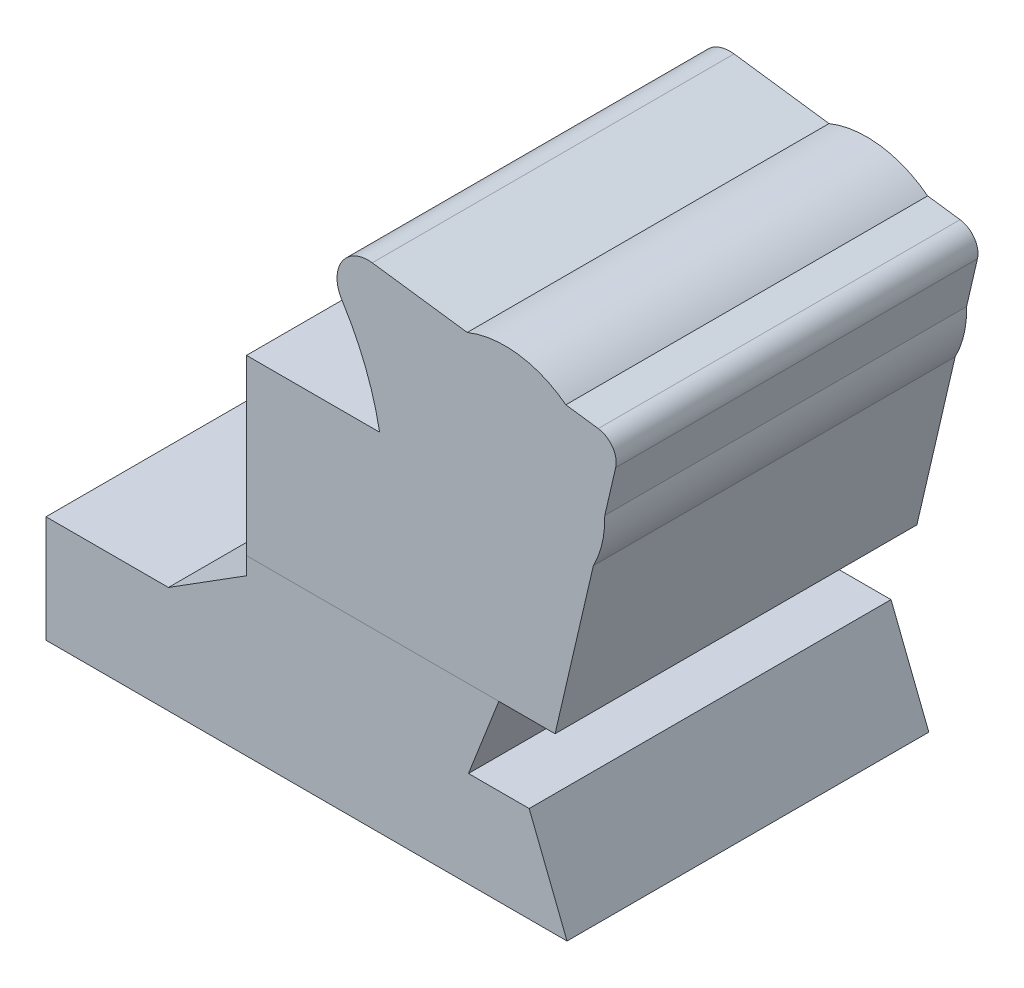
SolidWorks part; units mm, degrees
ref_plane "前视基准面" through (0, 0, 0) normal (0, 0, 1) x (1, 0, 0)
ref_plane "上视基准面" through (0, 0, 0) normal (0, 1, 0) x (1, 0, 0)
ref_plane "右视基准面" through (0, 0, 0) normal (1, 0, 0) x (0, 0, -1)
sketch "草图1" plane through (0, 0, 0) normal (0, 0, 1) x (1, 0, 0)
  line L1 (0, 29.5569) -> (33.8411, 29.5569)
  line L2 (116.7701, 26.4939) -> (125.1562, 47.9624)
  line L3 (152.6325, 126.9813) -> (90.1698, 135.4275)
  line L6 (89.0201, 126.9249) -> (126.841, 106.3205)
  line L8 (0, 0) -> (0, 29.5569)
  line L9 (33.8411, 29.5569) -> (55.4044, 43.1338)
  line L11 (144.001, 0) -> (133.5423, 26.4939)
  line L14 (89.661, -18.3061) -> (89.661, 35.0616) construction
  line L17 (125.1562, 47.9624) -> (140.6985, 47.9624)
  line L18 (140.6985, 47.9624) -> (157.4376, 120.0186)
  line L20 (133.5423, 26.4939) -> (116.7701, 26.4939)
  line L21 (55.4044, 43.1338) -> (55.4044, 95.8971)
  line L22 (0, 0) -> (144.001, 0)
  line L23 (55.4044, 95.8971) -> (92.2029, 95.8971)
  arc A2 (81.7861, 122.3112) -> (92.2029, 95.8971) centre (19.0918, 82.3258) cw
  arc A9 (90.1698, 135.4275) -> (81.7861, 122.3112) centre (89.0201, 126.9249) ccw
  arc A10 (157.4376, 120.0186) -> (152.6325, 126.9813) centre (151.866, 121.3129) ccw
  circle A15 centre (126.841, 106.3205) radius 27.6011
  dimension "D2" = 55.2022
  dimension "D3" = 74.36
  dimension "D4" = 8.58
  dimension "D5" = 5.72
  dimension "D1" = 106.3205
  dimension "D6" = 19.0918
  dimension "D7" = 33.8411
  dimension "D8" = 55.4044
  dimension "D9" = 81.7861
  dimension "D10" = 90.1698
  dimension "D11" = 89.661
  dimension "D12" = 151.866
  dimension "D13" = 92.2029
  dimension "D14" = 116.7701
  dimension "D15" = 125.1562
  dimension "D16" = 126.841
  dimension "D17" = 133.5423
  dimension "D18" = 140.6985
  dimension "D19" = 144.001
  dimension "D20" = 26.4939
  dimension "D21" = 29.5569
  dimension "D22" = 157.4376
  dimension "D23" = 43.1338
  dimension "D24" = 47.9624
extrude "凸台-拉伸1" add sketch "草图1" along normal mid plane 100
sketch "草图2" plane through (0, 0, 50) normal (0, 0, 1) x (1, 0, 0)
  line L0 (125.1562, 47.9624) -> (37.9215, 47.9624)
split "分割1" trim tools "草图2" bodies to split 106 resulting bodies 107 108
